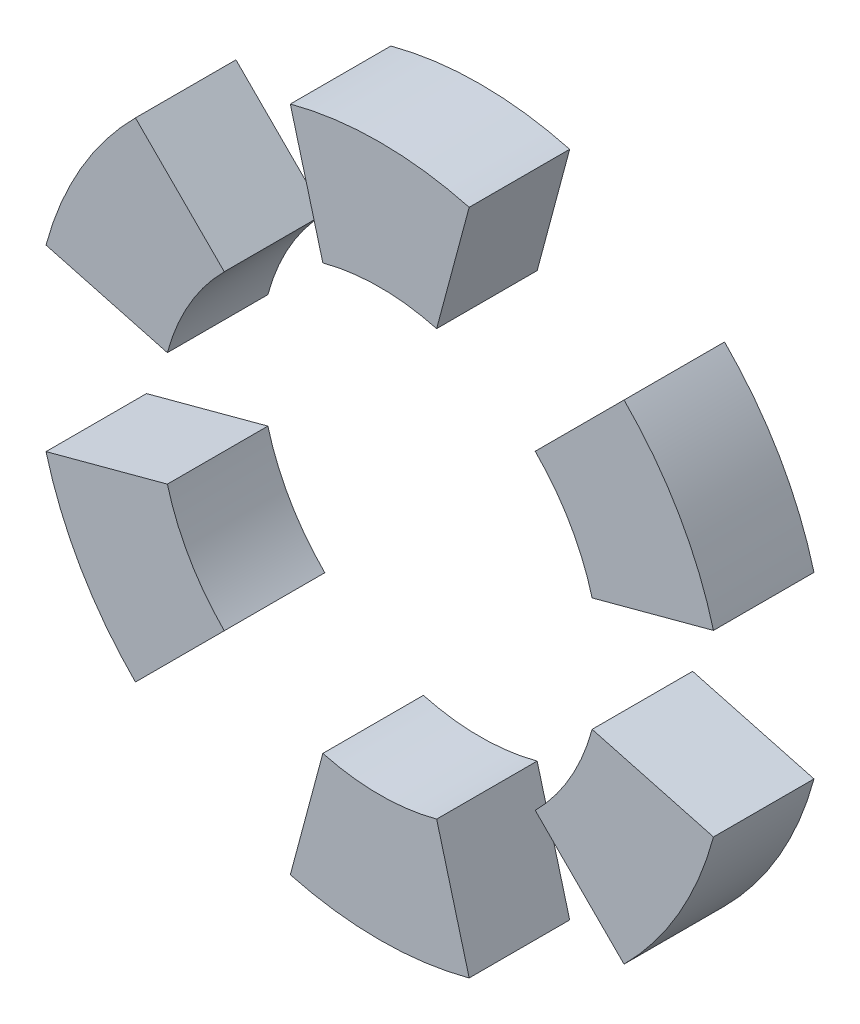
SolidWorks part; units mm, degrees
ref_plane "Front Plane" through (0, 0, 0) normal (0, 0, 1) x (1, 0, 0)
ref_plane "Top Plane" through (0, 0, 0) normal (0, 1, 0) x (1, 0, 0)
ref_plane "Right Plane" through (0, 0, 0) normal (1, 0, 0) x (0, 0, -1)
sketch "Sketch1" plane through (0, 0, 0) normal (0, 0, 1) x (1, 0, 0)
  line L0 (-4.5293, 16.9037) -> (-7.1175, 26.563)
  line L1 (4.5293, 16.9037) -> (7.1175, 26.563)
  line L2 (0, 0) -> (0, 27.2948) construction
  line L3 (12.3744, 12.3744) -> (19.4454, 19.4454)
  line L4 (16.9037, 4.5293) -> (26.563, 7.1175)
  line L5 (16.9037, -4.5293) -> (26.563, -7.1175)
  line L6 (12.3744, -12.3744) -> (19.4454, -19.4454)
  line L7 (4.5293, -16.9037) -> (7.1175, -26.563)
  line L8 (-4.5293, -16.9037) -> (-7.1175, -26.563)
  line L9 (-12.3744, -12.3744) -> (-19.4454, -19.4454)
  line L10 (-16.9037, -4.5293) -> (-26.563, -7.1175)
  line L11 (-16.9037, 4.5293) -> (-26.563, 7.1175)
  line L12 (-12.3744, 12.3744) -> (-19.4454, 19.4454)
  arc A0 (-16.9037, -4.5293) -> (-12.3744, -12.3744) centre (0, 0) ccw
  arc A1 (-26.563, -7.1175) -> (-19.4454, -19.4454) centre (0, 0) ccw
  circle A2 centre (0, 0) radius 17.5 construction
  arc A3 (4.5293, 16.9037) -> (-4.5293, 16.9037) centre (0, 0) ccw
  arc A4 (16.9037, 4.5293) -> (12.3744, 12.3744) centre (0, 0) ccw
  arc A5 (12.3744, -12.3744) -> (16.9037, -4.5293) centre (0, 0) ccw
  arc A6 (-4.5293, -16.9037) -> (4.5293, -16.9037) centre (0, 0) ccw
  circle A7 centre (0, 0) radius 27.5 construction
  arc A8 (-7.1175, -26.563) -> (7.1175, -26.563) centre (0, 0) ccw
  arc A9 (19.4454, -19.4454) -> (26.563, -7.1175) centre (0, 0) ccw
  arc A10 (26.563, 7.1175) -> (19.4454, 19.4454) centre (0, 0) ccw
  arc A11 (7.1175, 26.563) -> (-7.1175, 26.563) centre (0, 0) ccw
  arc A12 (-12.3744, 12.3744) -> (-16.9037, 4.5293) centre (0, 0) ccw
  arc A13 (-19.4454, 19.4454) -> (-26.563, 7.1175) centre (0, 0) ccw
  point P18 (0, 0)
  dimension "D1" = 35
  dimension "D3" = 15
  dimension "D4" = 15
  dimension "D2" = 10
  dimension "D5" = 6
extrude "Boss-Extrude1" add sketch "Sketch1" along normal blind 8
